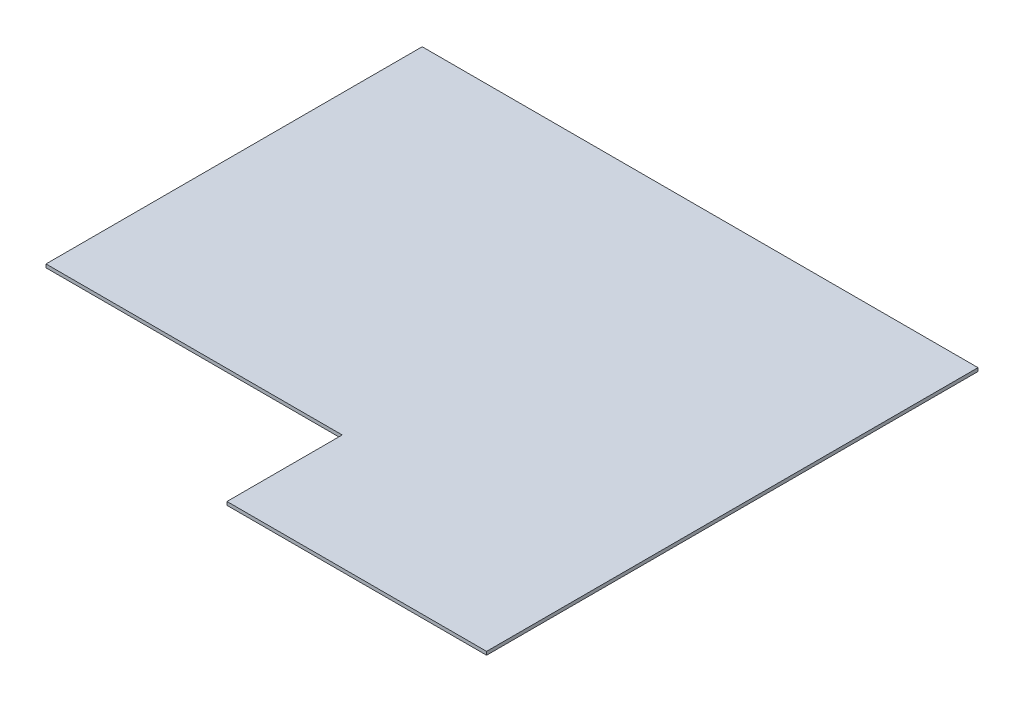
SolidWorks part; units mm, degrees
ref_plane "Спереди" through (0, 0, 0) normal (0, 0, 1) x (1, 0, 0)
ref_plane "Сверху" through (0, 0, 0) normal (0, 1, 0) x (1, 0, 0)
ref_plane "Справа" through (0, 0, 0) normal (1, 0, 0) x (0, 0, -1)
sketch "Эскиз1" plane through (0, 0, 0) normal (0, 1, 0) x (1, 0, 0)
  line L0 (0, 14500) -> (16400, 14500)
  line L1 (16400, 14500) -> (16400, 0)
  line L2 (16400, 0) -> (8740, 0)
  line L3 (8740, 0) -> (8740, 3400)
  line L4 (8740, 3400) -> (0, 3400)
  line L5 (0, 3400) -> (0, 14500)
  dimension "D1" = 7660
  dimension "D2" = 16400
  dimension "D3" = 14500
  dimension "D4" = 3400
extrude "Вытянуть1" add sketch "Эскиз1" along normal blind 100
